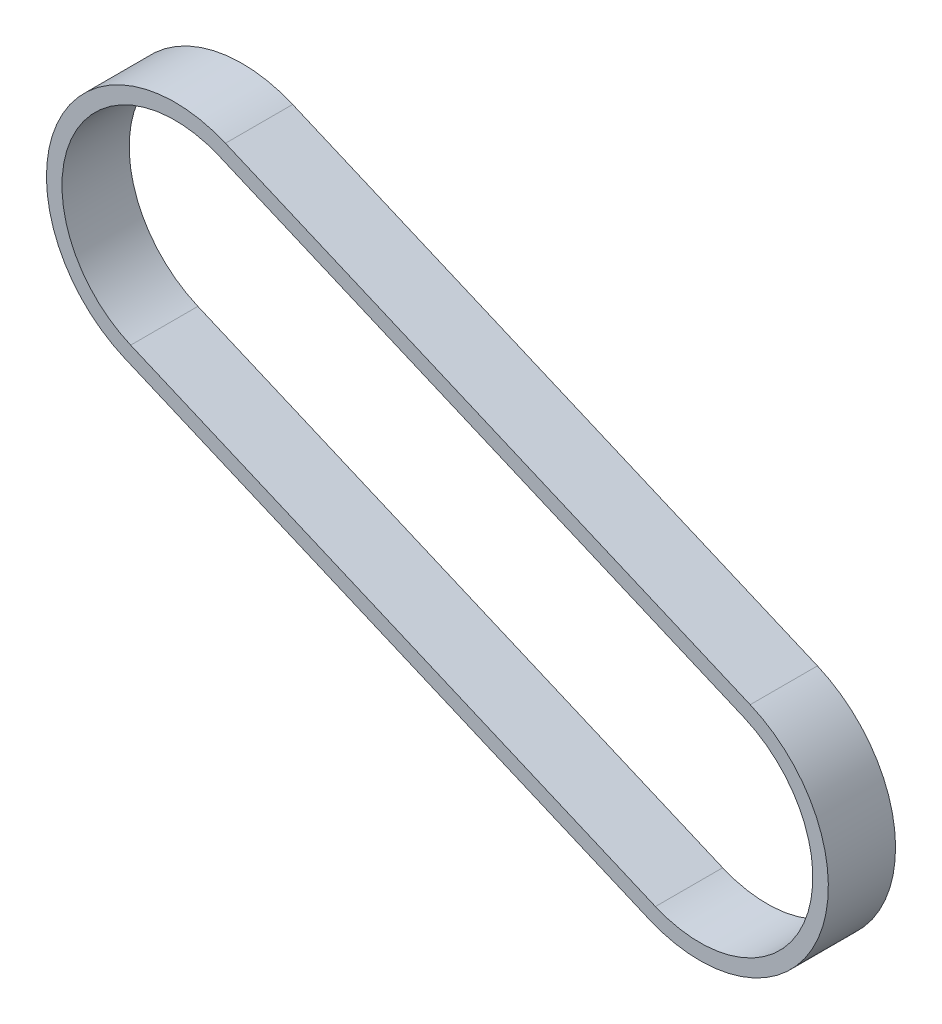
SolidWorks part; units mm, degrees
ref_plane "Front Plane" through (0, 0, 0) normal (0, 0, 1) x (1, 0, 0)
ref_plane "Top Plane" through (0, 0, 0) normal (0, 1, 0) x (1, 0, 0)
ref_plane "Right Plane" through (0, 0, 0) normal (1, 0, 0) x (0, 0, -1)
sketch "Sketch2" plane through (0, 0, 0) normal (0, 0, 1) x (1, 0, 0)
  line L0 (0, 0) -> (1, 0) construction
  line L1 (0, 0) -> (0, 1) construction
  line L2 (-7.5796, -16.1228) -> (-93.4672, 20.5067)
  line L3 (-78.9524, 54.5408) -> (6.9353, 17.9113)
  arc A0 (6.9353, 17.9113) -> (-7.5796, -16.1228) centre (-0.3221, 0.8943) cw
  arc A1 (-93.4672, 20.5067) -> (-78.9524, 54.5408) centre (-86.2098, 37.5238) cw
extrude "Extrude-Thin1" add sketch "Sketch2" against normal up to surface (11 mm away) thin thin type one direction wall 2.54
